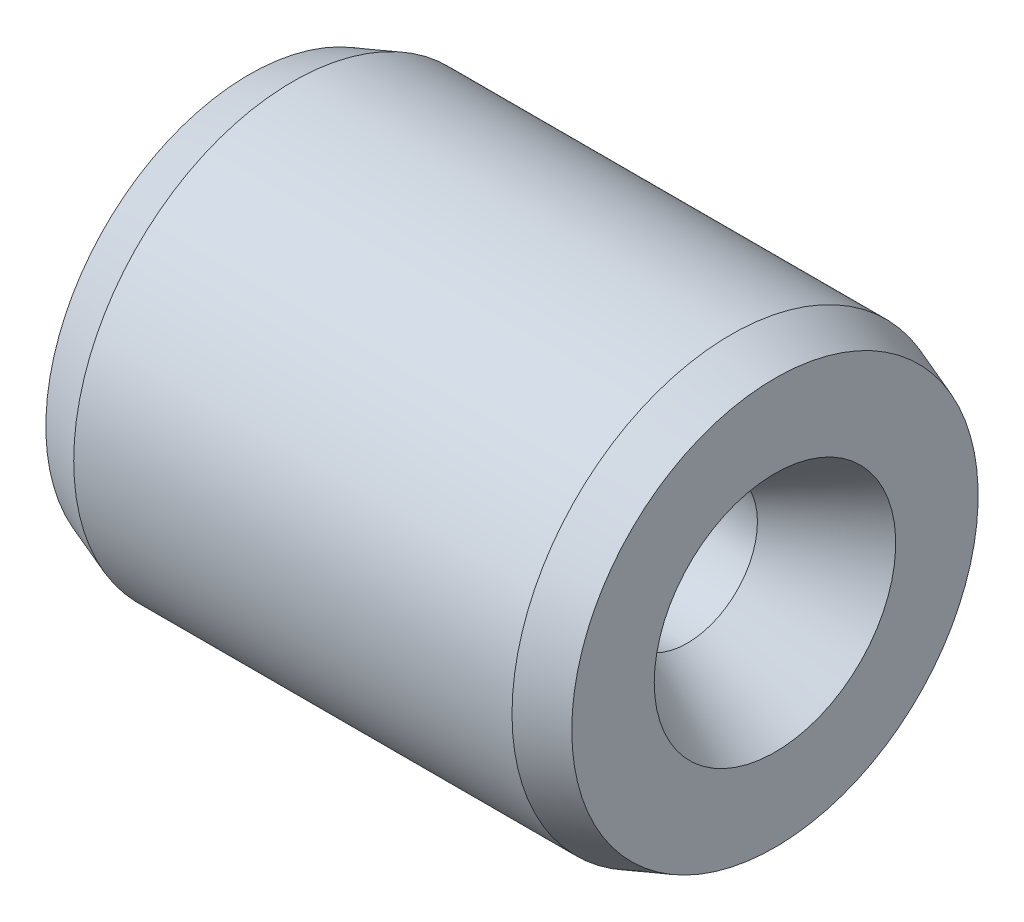
SolidWorks part; units mm, degrees
material "1.4301 (X5CrNi18-10)"
ref_plane "Vorne" through (0, 0, 0) normal (0, 0, 1) x (1, 0, 0)
ref_plane "Oben" through (0, 0, 0) normal (0, 1, 0) x (1, 0, 0)
ref_plane "Rechts" through (0, 0, 0) normal (1, 0, 0) x (0, 0, -1)
sketch "Skizze1" plane through (0, 0, 0) normal (0, 0, 1) x (1, 0, 0)
  line L0 (0, 0) -> (14.5258, 0) construction
  line L2 (0, 0.5) -> (6, 0.5)
  line L3 (0, 0.5) -> (0, 2.5)
  line L4 (0, 2.5) -> (6, 2.5)
  line L5 (6, 0.5) -> (6, 2.5)
  dimension "D1" = 1
  dimension "D2" = 5
  dimension "D3" = 6
revolve "Rotation1" add sketch "Skizze1" angle 360 about L0
hole_wizard "M2 Gewindebohrung1" positions "Skizze3" profile "Skizze2" tap size "M2" standard "DIN" end condition through all
sketch "Skizze3" plane through (6, 0, 0) normal (1, 0, 0) x (0, 0, -1)
  point P0 (0, 0)
cosmetic thread "Bohrungsgewinde1" parameters "D2"=2
sketch "Skizze2" plane through (6, 0, 0) normal (0, 1, 0) x (0, 0, -1)
  line L0 (0, 0) -> (0, 6)
  line L1 (0, 6) -> (0.8, 6)
  line L2 (0.8, 6) -> (0.8, 0)
  line L5 (0.8, 0) -> (0, 0)
  line L11 (0, -6.35) -> (0, 107.95) construction
  dimension "Bohrerdurchmesser" = 1.6
  dimension "Bohrungstiefe" = 6
chamfer "Fase1" distance 0.5 angle 20 2 edges at (0, 0, 2.5) (6, 0, 2.5)
chamfer "Fase2" distance 1 angle 30 2 edges at (6, 0, -0.8) (0, 0, -0.8)
